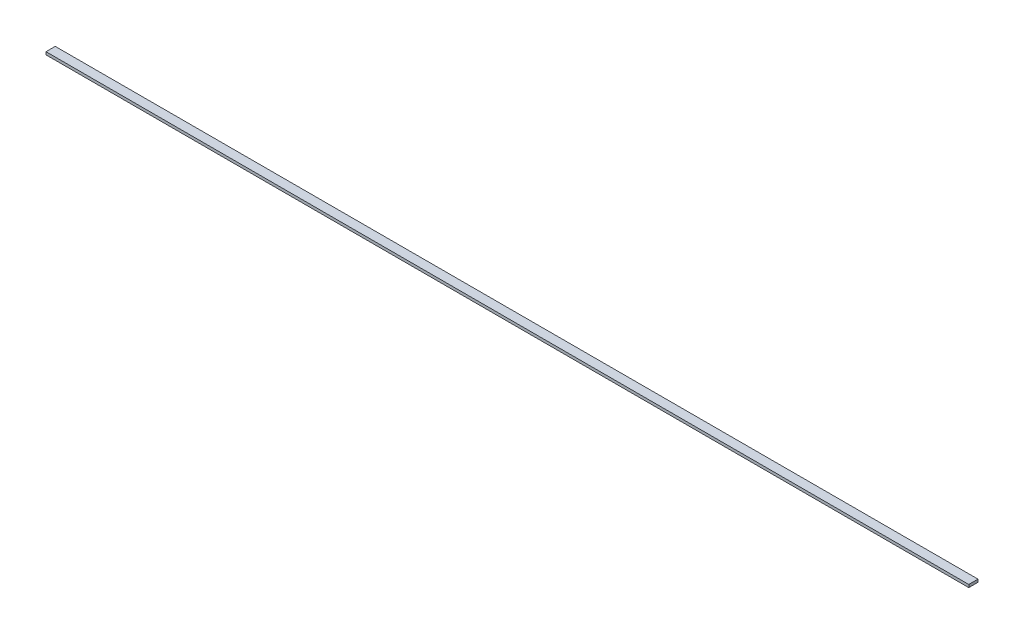
SolidWorks part; units mm, degrees
ref_plane "Front Plane" through (0, 0, 0) normal (0, 0, 1) x (1, 0, 0)
ref_plane "Top Plane" through (0, 0, 0) normal (0, 1, 0) x (1, 0, 0)
ref_plane "Right Plane" through (0, 0, 0) normal (1, 0, 0) x (0, 0, -1)
sketch "Sketch1" plane through (0, 0, 0) normal (0, 1, 0) x (1, 0, 0)
  line L0 (0, 0) -> (1000, 0)
  line L1 (0, 0) -> (0, 10)
  line L2 (0, 10) -> (1000, 10)
  line L3 (1000, 10) -> (1000, 0)
  dimension "D1" = 1000
  dimension "D2" = 10
extrude "Boss-Extrude1" add sketch "Sketch1" along normal blind 3
